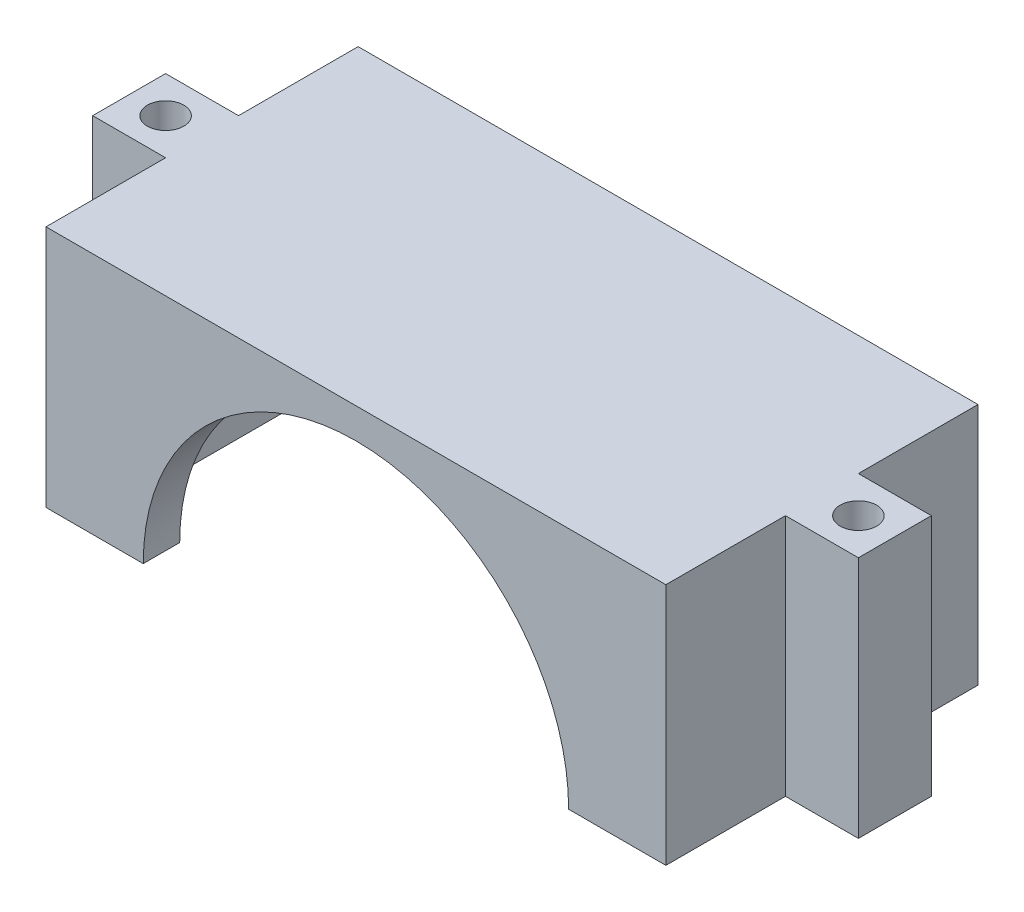
SolidWorks part; units mm, degrees
ref_plane "Front" through (0, 0, 0) normal (0, 0, 1) x (1, 0, 0)
ref_plane "Top" through (0, 0, 0) normal (0, 1, 0) x (1, 0, 0)
ref_plane "Right" through (0, 0, 0) normal (1, 0, 0) x (0, 0, -1)
sketch "Sketch1" plane through (0, 0, 0) normal (0, 1, 0) x (1, 0, 0)
  line L1 (-22.5, -9.84) -> (22.5, -9.84) construction
  line L2 (-22.5, -9.84) -> (-22.5, 9.84) construction
  line L3 (-22.5, 9.84) -> (22.5, 9.84) construction
  line L4 (22.5, -9.84) -> (22.5, 9.84) construction
  line L5 (-22.5, -9.84) -> (22.5, 9.84) construction
  line L6 (-22.5, 9.84) -> (22.5, -9.84) construction
  line L7 (-25.5, -12.84) -> (25.5, -12.84)
  line L8 (-25.5, -12.84) -> (-25.5, 12.84)
  line L9 (-25.5, 12.84) -> (25.5, 12.84)
  line L10 (25.5, -12.84) -> (25.5, 12.84)
  line L11 (-25.5, -12.84) -> (25.5, 12.84) construction
  line L12 (-25.5, 12.84) -> (25.5, -12.84) construction
  point P1 (0, 0)
  point P6 (0, 0)
  dimension "D1" = 45
  dimension "D2" = 19.68
  dimension "D3" = 3
  dimension "D4" = 3
extrude "Boss-Extrude1" add sketch "Sketch1" along normal blind 20
sketch "Sketch3" plane through (0, 0, 0) normal (0, -1, 0) x (1, 0, 0)
  line L1 (-22.5, -9.84) -> (22.5, -9.84)
  line L2 (-22.5, -9.84) -> (-22.5, 9.84)
  line L3 (-22.5, 9.84) -> (22.5, 9.84)
  line L4 (22.5, -9.84) -> (22.5, 9.84)
  line L5 (-22.5, -9.84) -> (22.5, 9.84) construction
  line L6 (-22.5, 9.84) -> (22.5, -9.84) construction
  point P0 (0, 0)
  dimension "D1" = 19.68
  dimension "D2" = 45
extrude "Cut-Extrude1" cut sketch "Sketch3" against normal blind 17.5
sketch "Sketch4" plane through (0, 0, 12.84) normal (0, 0, 1) x (1, 0, 0)
  line L0 (-25.5, 0) -> (25.5, 0) construction
  line L2 (-17.5, 0) -> (17.5, 0)
  arc A0 (17.5, 0) -> (-17.5, 0) centre (0, 0) ccw
  dimension "D1" = 35
extrude "Cut-Extrude2" cut sketch "Sketch4" against normal up to surface (3 mm away) up to face at (0, 8.75, 9.84)
sketch "Sketch5" plane through (0, 0, -12.84) normal (0, 0, -1) x (-1, 0, 0)
  line L0 (-25.5, 0) -> (25.5, 0) construction
  line L1 (-22, 0) -> (-12, 0)
  line L2 (-22, 0) -> (-22, 6)
  line L3 (-22, 6) -> (-12, 6)
  line L4 (-12, 0) -> (-12, 6)
  line L5 (-25.5, 20) -> (-25.5, 0) construction
  dimension "D1" = 3.5
  dimension "D2" = 6
  dimension "D3" = 10
extrude "Cut-Extrude3" cut sketch "Sketch5" against normal up to surface (3 mm away) up to face at (0, 8.75, -9.84)
sketch "Sketch6" plane through (0, 0, 0) normal (0, -1, 0) x (1, 0, 0)
  line L0 (25.5, 12.84) -> (25.5, -12.84) construction
  line L1 (-25.5, -12.84) -> (-25.5, 12.84) construction
  line L2 (0, 0) -> (25.5, 0) construction
  line L3 (25.5, -3) -> (31.5, -3)
  line L4 (25.5, -3) -> (25.5, 3)
  line L5 (25.5, 3) -> (31.5, 3)
  line L6 (31.5, -3) -> (31.5, 3)
  line L7 (0, 0) -> (0, -5.7895) construction
  line L8 (-25.5, 3) -> (-31.5, 3)
  line L9 (-25.5, -3) -> (-25.5, 3)
  line L10 (-25.5, -3) -> (-31.5, -3)
  line L11 (-31.5, -3) -> (-31.5, 3)
  circle A0 centre (28.5, 0) radius 1.5
  circle A1 centre (-28.5, 0) radius 1.5
  point P0 (25.5, 0)
  point P1 (-25.5, 0)
  point P4 (25.5, -3)
  point P14 (28.5, 0)
  dimension "D5" = 3
  dimension "D1" = 3
  dimension "D2" = 6
  dimension "D3" = 6
  dimension "D4" = 3
extrude "Boss-Extrude2" add sketch "Sketch6" against normal blind 20
